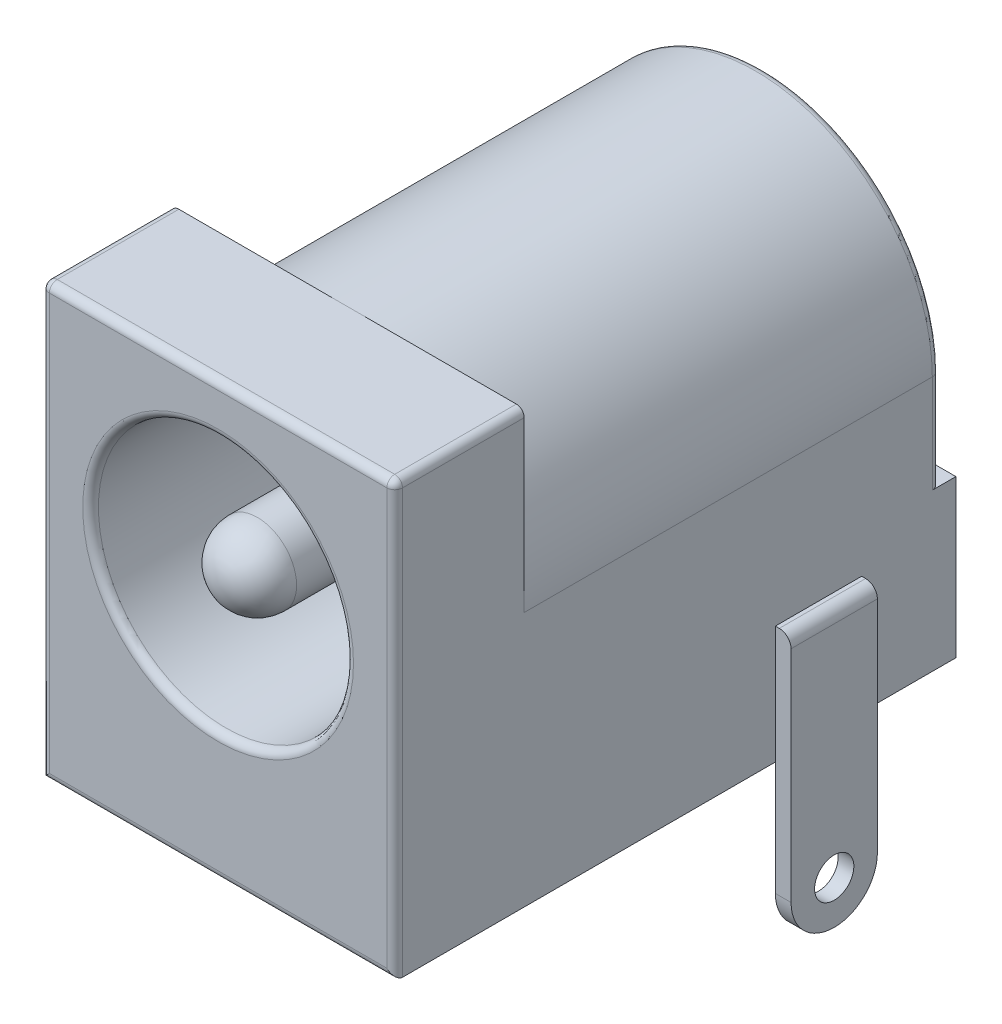
SolidWorks part; units mm, degrees
ref_plane "Front Plane" through (0, 0, 0) normal (0, 0, 1) x (1, 0, 0)
ref_plane "Top Plane" through (0, 0, 0) normal (0, 1, 0) x (1, 0, 0)
ref_plane "Right Plane" through (0, 0, 0) normal (1, 0, 0) x (0, 0, -1)
sketch "Sketch1" plane through (0, 0, 0) normal (0, 0, 1) x (1, 0, 0)
  line L1 (-4.5, 5.5) -> (4.5, 5.5)
  line L2 (-4.5, 5.5) -> (-4.5, -5.5)
  line L3 (-4.5, -5.5) -> (4.5, -5.5)
  line L4 (4.5, 5.5) -> (4.5, -5.5)
  line L5 (-4.5, 5.5) -> (4.5, -5.5) construction
  line L6 (-4.5, -5.5) -> (4.5, 5.5) construction
  point P0 (0, 0)
  dimension "D1" = 11
  dimension "D2" = 9
extrude "Boss-Extrude1" add sketch "Sketch1" against normal blind 3.3
sketch "Sketch2" plane through (0, 0, -3.3) normal (0, 0, -1) x (-1, 0, 0)
  line L0 (-4.5, -5.5) -> (4.5, -5.5)
  line L1 (4.5, -5.5) -> (4.5, 1)
  line L2 (4.5, 5.5) -> (4.5, -5.5) construction
  line L3 (-4.5, -5.5) -> (-4.5, 5.5) construction
  line L4 (-4.5, 1) -> (-4.5, -5.5)
  line L5 (-4.5, 5.5) -> (4.5, 5.5) construction
  arc A0 (4.5, 1) -> (-4.5, 1) centre (0, 1) ccw
extrude "Boss-Extrude2" add sketch "Sketch2" along normal blind 11
sketch "Sketch3" plane through (0, 0, 0) normal (0, 0, 1) x (1, 0, 0)
  line L0 (-4.5, -5.5) -> (4.5, -5.5) construction
  circle A0 centre (0, 1) radius 3.25
  point P4 (0, 0)
  dimension "D1" = 6.5
  dimension "D2" = 6.5
extrude "Cut-Extrude1" cut sketch "Sketch3" against normal blind 11
sketch "Sketch4" plane through (0, 0, -11) normal (0, 0, 1) x (1, 0, 0)
  circle A0 centre (0, 1) radius 1
  circle A1 centre (0, 1) radius 3.25 construction
  point P2 (0, 1.0127)
  dimension "D1" = 2
extrude "Boss-Extrude3" add sketch "Sketch4" along normal blind 11
fillet "Fillet1" radius 1 1 edges at (1, 1, 0)
fillet "Fillet2" radius 0.2 7 edges at (0, -5.5, 0) (-4.5, 0, 0) (0, 5.5, 0) (4.5, 0, 0) (3.25, 1, 0) (-4.5, 5.5, -1.65) (4.5, 5.5, -1.65)
sketch "Sketch5" plane through (0, 0, -14.3) normal (0, 0, -1) x (-1, 0, 0)
  line L0 (4.5, -5.5) -> (4.5, 1) construction
  line L1 (4.5, -1.5) -> (1.2, -1.5)
  line L2 (4.5, -1.5) -> (4.5, 5.5)
  line L3 (4.5, 5.5) -> (-4.5, 5.5)
  line L4 (-4.5, -1.5) -> (-4.5, 5.5)
  line L5 (-4.5, 1) -> (-4.5, -5.5) construction
  line L6 (-1.2, -1.5) -> (-1.2, -5.5)
  line L7 (-4.5, -5.5) -> (4.5, -5.5) construction
  line L8 (-1.2, -5.5) -> (1.2, -5.5)
  line L9 (1.2, -5.5) -> (1.2, -1.5)
  line L10 (-1.2, -1.5) -> (-4.5, -1.5)
  arc A0 (4.5, 1) -> (-4.5, 1) centre (0, 1) ccw construction
  dimension "D1" = 2.4
  dimension "D2" = 4
extrude "Cut-Extrude2" cut sketch "Sketch5" against normal blind 0.4
sketch "Sketch6" plane through (0, 0, -13.9) normal (0, 0, -1) x (-1, 0, 0)
  line L0 (0, -8.4) -> (0, 1) construction
  line L1 (-1.1, -8.4) -> (-1.1, 1)
  line L2 (1.1, -8.4) -> (1.1, 1)
  line L3 (1.2, -5.5) -> (4.5, -5.5) construction
  arc A0 (-1.1, -8.4) -> (1.1, -8.4) centre (0, -8.4) ccw
  arc A1 (1.1, 1) -> (-1.1, 1) centre (0, 1) ccw
  arc A2 (4.5, 1) -> (-4.5, 1) centre (0, 1) ccw construction
  circle A3 centre (0, -8.4) radius 0.5
  circle A4 centre (0, 1) radius 0.5
  point P3 (0, -3.7)
  point P13 (0, -9.5)
  dimension "D1" = 1.1
  dimension "D3" = 1
  dimension "D2" = 4
extrude "Boss-Extrude4" add sketch "Sketch6" along normal blind 0.4
sketch "Sketch7" plane through (0, 0, -14.3) normal (0, 0, -1) x (-1, 0, 0)
  circle A0 centre (0, 1) radius 1.9
  circle A1 centre (0, 1) radius 0.5
  dimension "D1" = 3.8
extrude "Boss-Extrude5" add sketch "Sketch7" against normal blind 0.4
ref_plane "Plane1" through (0, 0, -8.1) normal (0, 0, -1) x (-1, 0, 0)
sketch "Sketch8" plane through (0, 0, -8.1) normal (0, 0, -1) x (-1, 0, 0)
  line L0 (-1.1, -5.1452) -> (-1.1, -8.4)
  line L1 (1.1, -8.4) -> (1.1, -5.1452)
  line L2 (1.1, -5.1452) -> (-1.1, -5.1452)
  line L3 (1.1, -8.4) -> (1.1, -0.5492) construction
  arc A0 (-1.1, -8.4) -> (1.1, -8.4) centre (0, -8.4) ccw
  circle A1 centre (0, -8.4) radius 0.5
  circle A2 centre (0, -8.4) radius 0.5 construction
  arc A3 (-1.1, -8.4) -> (1.1, -8.4) centre (0, -8.4) ccw construction
  point P6 (0, -8.4)
  point P13 (1.1, -5.1452)
extrude "Boss-Extrude6" add sketch "Sketch8" against normal blind 0.4
sketch "Sketch9" plane through (4.5, 0, 0) normal (1, 0, 0) x (0, 0, -1)
  line L0 (9.7, -2.5) -> (9.7, -8.4)
  line L1 (11.9, -8.4) -> (11.9, -2.5)
  line L2 (11.9, -2.5) -> (9.7, -2.5)
  line L3 (13.9, -9.5) -> (14.3, -9.5) construction
  line L4 (7.9, -9.5) -> (14.1, -9.5) construction
  line L5 (7.7, -9.5) -> (8.1, -9.5) construction
  line L6 (0, -5.3) -> (0, 5.3) construction
  line L7 (14.3, -5.5) -> (0.2, -5.5) construction
  arc A0 (9.7, -8.4) -> (11.9, -8.4) centre (10.8, -8.4) ccw
  circle A1 centre (10.8, -8.4) radius 0.5
  point P5 (10.8, -9.5)
  point P13 (9.676, -8.4)
  dimension "D1" = 1
  dimension "D2" = 1.1
  dimension "D3" = 10.8
  dimension "D4" = 3
extrude "Boss-Extrude7" add sketch "Sketch9" along normal blind 0.4
sketch "Sketch10" plane through (0, 0, -11) normal (0, 0, 1) x (1, 0, 0)
  line L1 (-1.4, -2.75) -> (1.4, -2.75)
  line L2 (-1.4, -2.75) -> (-1.4, -1.75)
  line L3 (-1.4, -1.75) -> (1.4, -1.75)
  line L4 (1.4, -2.75) -> (1.4, -1.75)
  line L5 (-1.4, -2.75) -> (1.4, -1.75) construction
  line L6 (-1.4, -1.75) -> (1.4, -2.75) construction
  circle A0 centre (0, 1) radius 3.25 construction
  point P0 (0, -2.25)
  dimension "D1" = 2.8
  dimension "D2" = 0.5
extrude "Boss-Extrude8" add sketch "Sketch10" along normal blind 6.4
fillet "Fillet3" radius 0.3 2 edges at (4.9, -2.5, -10.8) (0, -1.75, -4.6)
fillet "Fillet4" radius 0.2 3 edges at (-4.5, -0.25, -13.9) (4.5, -0.25, -13.9) (0, 5.5, -13.9)
